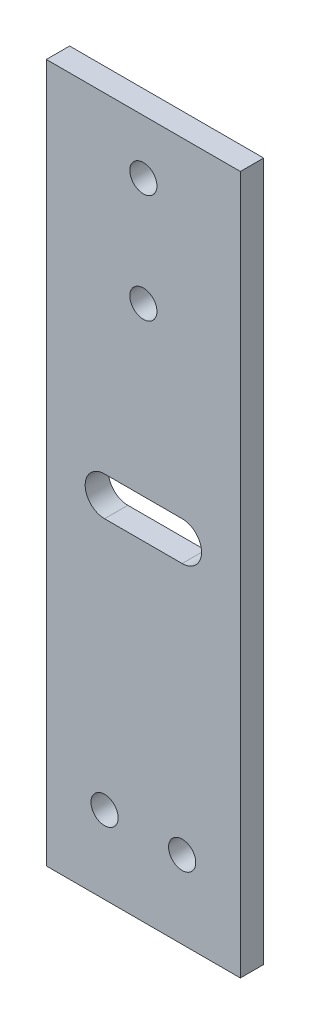
SolidWorks part; units mm, degrees
ref_plane "前视基准面" through (0, 0, 0) normal (0, 0, 1) x (1, 0, 0)
ref_plane "上视基准面" through (0, 0, 0) normal (0, 1, 0) x (1, 0, 0)
ref_plane "右视基准面" through (0, 0, 0) normal (1, 0, 0) x (0, 0, -1)
other "Configuration Table"
sketch "草图1" plane through (0, 0, 0) normal (0, 0, 1) x (1, 0, 0)
  line L1 (-12.5, 45) -> (12.5, 45)
  line L2 (-12.5, 45) -> (-12.5, -45)
  line L3 (-12.5, -45) -> (12.5, -45)
  line L4 (12.5, 45) -> (12.5, -45)
  line L5 (-12.5, 45) -> (12.5, -45) construction
  line L6 (-12.5, -45) -> (12.5, 45) construction
  point P0 (0, 0)
  dimension "D1" = 25
  dimension "D2" = 90
extrude "凸台-拉伸1" add sketch "草图1" along normal blind 3
sketch "草图3" plane through (0, 0, 3) normal (0, 0, 1) x (1, 0, 0)
  line L0 (0, 45) -> (0, -45) construction
  line L1 (12.5, 45) -> (-12.5, 45) construction
  line L2 (-12.5, -45) -> (12.5, -45) construction
  line L3 (-12.5, 38) -> (12.5, 38) construction
  line L4 (-12.5, 45) -> (-12.5, -45) construction
  line L5 (12.5, -45) -> (12.5, 45) construction
  line L6 (-12.5, 24) -> (12.5, 24) construction
  line L7 (-12.5, -35) -> (12.5, -35) construction
  line L8 (5, -45) -> (5, 45) construction
  line L9 (-5, 45) -> (-5, -45) construction
  circle A0 centre (0, 38) radius 1.75
  circle A1 centre (0, 24) radius 1.75
  circle A2 centre (-5, -35) radius 1.75
  circle A3 centre (5, -35) radius 1.75
  point P14 (0, 38)
  point P15 (0, 24)
  point P26 (-5, -35)
  point P27 (5, -35)
  dimension "D3" = 3.5
  dimension "D7" = 3.5
  dimension "D1" = 14
  dimension "D2" = 7
  dimension "D4" = 10
  dimension "D5" = 7.5
  dimension "D6" = 10
extrude "切除-拉伸1" cut sketch "草图3" against normal through all
sketch "草图4" plane through (0, 0, 3) normal (0, 0, 1) x (1, 0, 0)
  line L0 (-12.5, 0) -> (12.5, 0) construction
  line L1 (-12.5, 45) -> (-12.5, -45) construction
  line L2 (12.5, -45) -> (12.5, 45) construction
  line L3 (0, 45) -> (0, -45) construction
  line L4 (12.5, 45) -> (-12.5, 45) construction
  line L5 (-12.5, -45) -> (12.5, -45) construction
  line L6 (-5, 0) -> (5, 0) construction
  line L7 (-5, 2.5) -> (5, 2.5)
  line L8 (-5, -2.5) -> (5, -2.5)
  arc A0 (-5, 2.5) -> (-5, -2.5) centre (-5, 0) ccw
  arc A1 (5, -2.5) -> (5, 2.5) centre (5, 0) ccw
  point P14 (0, 0)
  dimension "D2" = 10
  dimension "D1" = 5
extrude "切除-拉伸2" cut sketch "草图4" against normal through all
